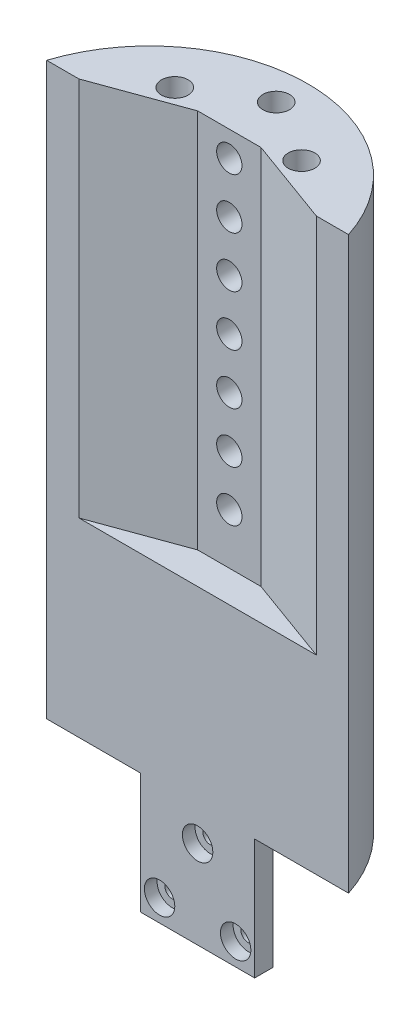
SolidWorks part; units mm, degrees
ref_plane "Front Plane" through (0, 0, 0) normal (0, 0, 1) x (1, 0, 0)
ref_plane "Top Plane" through (0, 0, 0) normal (0, 1, 0) x (1, 0, 0)
ref_plane "Right Plane" through (0, 0, 0) normal (1, 0, 0) x (0, 0, -1)
sketch "Sketch1" plane through (0, 0, 0) normal (0, 1, 0) x (1, 0, 0)
  line L1 (-30.2473, -9.652) -> (30.2473, -9.652)
  line L2 (-30.2473, -9.652) -> (-30.2473, 9.652)
  line L3 (-30.2473, 9.652) -> (30.2473, 9.652)
  line L4 (30.2473, -9.652) -> (30.2473, 9.652)
  line L5 (-30.2473, -9.652) -> (30.2473, 9.652) construction
  line L6 (-30.2473, 9.652) -> (30.2473, -9.652) construction
  circle A0 centre (0, 0) radius 31.75
  dimension "D1" = 63.5
  dimension "D2" = 19.304
extrude "Boss-Extrude1" add sketch "Sketch1" along normal mid plane 114.3 contours L3 A0
sketch "Sketch2" plane through (0, -57.15, 0) normal (0, -1, 0) x (1, 0, 0)
  line L1 (-11.43, -9.525) -> (11.43, -9.525)
  line L2 (-11.43, -9.525) -> (-11.43, -13.335)
  line L3 (-11.43, -13.335) -> (11.43, -13.335)
  line L4 (12.7, -9.525) -> (-12.7, -9.525)
  line L5 (12.7, -14.605) -> (12.7, -9.525)
  line L6 (-12.7, -14.605) -> (12.7, -14.605)
  line L7 (-12.7, -9.525) -> (-12.7, -14.605)
  line L8 (12.7, -9.525) -> (-12.7, -9.525)
  line L9 (12.7, -14.605) -> (12.7, -9.525)
  line L10 (-12.7, -14.605) -> (12.7, -14.605)
  line L11 (-12.7, -9.525) -> (-12.7, -14.605)
  line L12 (11.43, -9.525) -> (11.43, -13.335)
  line M5 (30.2473, -9.652) -> (-30.2473, -9.652)
  dimension "D2" = 1.27
  dimension "D3" = 1.27
  dimension "D4" = 1.27
  dimension "D1" = 0
extrude "Boss-Extrude2" add sketch "Sketch2" along normal blind 24.13 contours L12 L2 L3 M5
sketch "Sketch3" plane through (0, 0, -9.652) normal (0, 0, 1) x (1, 0, 0)
  line L0 (11.43, -81.28) -> (11.43, -57.15) construction
  line L3 (0, -63.6412) -> (-7.62, -76.8395) construction
  line L4 (-7.62, -76.8395) -> (7.62, -76.8395) construction
  line L5 (7.62, -76.8395) -> (0, -63.6412) construction
  line L7 (11.43, -81.28) -> (-11.43, -81.28) construction
  circle A0 centre (0, -63.6412) radius 3.048
  circle A1 centre (-7.62, -76.8395) radius 3.048
  circle A2 centre (7.62, -76.8395) radius 3.048
  dimension "D2" = 6.096
  dimension "D3" = 6.096
  dimension "D4" = 6.096
  dimension "D1" = 15.24
  dimension "D5" = 11.43
  dimension "D6" = 4.4405
extrude "Cut-Extrude1" cut sketch "Sketch3" against normal blind 2.54
hole_wizard "Ø3.0mm Dowel Hole1" positions "Sketch4" profile "Sketch5" hole size "Ø3.0" standard "ANSI Metric" end condition through all
sketch "Sketch4" plane through (0, 0, -9.652) normal (0, 0, 1) x (1, 0, 0)
  point P0 (0, -63.6412)
  point P3 (7.62, -76.8395)
  point P6 (-7.62, -76.8395)
sketch "Sketch5" plane through (0, -63.6412, -9.652) normal (1, 0, 0) x (0, -1, 0)
  line L0 (0, 0) -> (0, 22.098)
  line L1 (0, 22.098) -> (1.5, 22.098)
  line L2 (1.5, 22.098) -> (1.5, 0)
  line L5 (1.5, 0) -> (0, 0)
  line L11 (0, -6.35) -> (0, 107.95) construction
  dimension "Thru Hole Dia." = 3
  dimension "Thru Hole Depth" = 22.098
sketch "Sketch6" plane through (0, 0, -9.652) normal (0, 0, 1) x (1, 0, 0)
  line L0 (-30.2473, 57.15) -> (30.2473, 57.15) construction
  line L1 (6.35, 57.15) -> (-6.35, 57.15)
  line L2 (6.35, 57.15) -> (6.35, -19.05)
  line L3 (6.35, -19.05) -> (-6.35, -19.05)
  line L4 (-6.35, 57.15) -> (-6.35, -19.05)
  dimension "D1" = 6.35
  dimension "D2" = 6.35
  dimension "D3" = 76.2
extrude "Cut-Extrude2" cut sketch "Sketch6" against normal blind 6.35
sketch "Sketch7" plane through (0, 0, -16.002) normal (0, 0, 1) x (1, 0, 0)
  line L0 (6.35, 57.15) -> (-6.35, 57.15) construction
  circle A0 centre (0, 52.07) radius 2.54
  circle A1 centre (0, 41.91) radius 2.54
  circle A2 centre (0, 31.75) radius 2.54
  circle A3 centre (0, 21.59) radius 2.54
  circle A4 centre (0, 11.43) radius 2.54
  circle A5 centre (0, 1.27) radius 2.54
  circle A6 centre (0, -8.89) radius 2.54
  dimension "D1" = 5.08
  dimension "D2" = 5.08
  dimension "D3" = 7
sketch "Sketch8" plane through (0, 57.15, 0) normal (0, 1, 0) x (1, 0, 0)
  line L0 (0, 25.4) -> (-12.7, 17.78)
  line L1 (-12.7, 17.78) -> (12.7, 17.78)
  line L2 (12.7, 17.78) -> (0, 25.4)
  circle A0 centre (0, 25.4) radius 2.667
  circle A1 centre (-12.7, 17.78) radius 2.667
  circle A2 centre (12.7, 17.78) radius 2.667
  dimension "D4" = 5.334
  dimension "D5" = 5.334
  dimension "D6" = 5.334
  dimension "D1" = 25.4
  dimension "D2" = 25.4
  dimension "D3" = 7.62
extrude "Cut-Extrude3" cut sketch "Sketch8" against normal blind 5.08 contours L2 A0 L0 | L0 A0 L2 | L0 A1 L1 | L1 A1 L0 | L2 A2 L1 | L1 A2 L2
extrude "Cut-Extrude4" cut sketch "Sketch7" against normal blind 6.35
sketch "Sketch9" plane through (0, 57.15, 0) normal (0, 1, 0) x (1, 0, 0)
  line L0 (6.35, 16.002) -> (23.7965, 9.652)
  line L1 (6.35, 9.652) -> (30.2473, 9.652) construction
  line L2 (-6.35, 16.002) -> (-23.7965, 9.652)
  line L3 (-30.2473, 9.652) -> (-6.35, 9.652) construction
  line L4 (-6.35, 16.002) -> (-6.35, 9.652) construction
  line L5 (6.35, 16.002) -> (6.35, 9.652) construction
  line L6 (-23.7965, 9.652) -> (-6.35, 9.652)
  line L7 (-6.35, 9.652) -> (-6.35, 16.002)
  line L8 (6.35, 16.002) -> (6.35, 9.652)
  line L9 (6.35, 9.652) -> (23.7965, 9.652)
  dimension "D1" = 70
  dimension "D2" = 70
extrude "Cut-Extrude5" cut sketch "Sketch9" against normal up to surface (76.2 mm away) up to face at (0, -19.05, -12.827)
